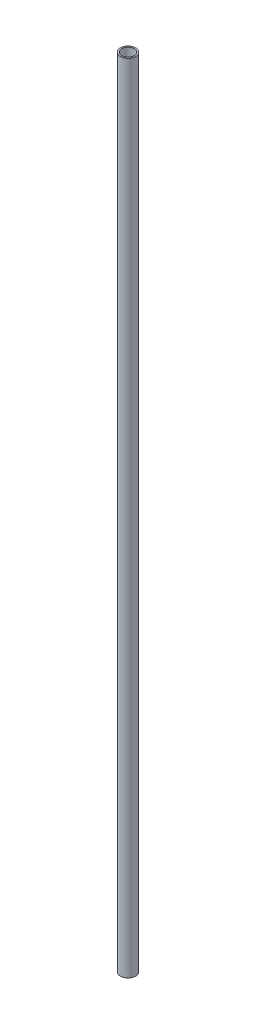
SolidWorks part; units mm, degrees
ref_plane "Front Plane" through (0, 0, 0) normal (0, 0, 1) x (1, 0, 0)
ref_plane "Top Plane" through (0, 0, 0) normal (0, 1, 0) x (1, 0, 0)
ref_plane "Right Plane" through (0, 0, 0) normal (1, 0, 0) x (0, 0, -1)
sketch "Sketch1" plane through (0, 0, 0) normal (0, 0, 1) x (1, 0, 0)
  line L0 (0, 0) -> (3.8735, 0) construction
  line L1 (3.8735, 0) -> (4.7625, 0)
  line L2 (4.7625, 0) -> (4.7625, 500)
  line L3 (4.7625, 500) -> (3.8735, 500)
  line L4 (3.8735, 500) -> (3.8735, 0)
  line L5 (0, 0) -> (0, 55.2819) construction
  dimension "D1" = 500
  dimension "D2" = 0.889
  dimension "D3" = 3.8735
revolve "Revolve1" add sketch "Sketch1" angle 360 about L5
